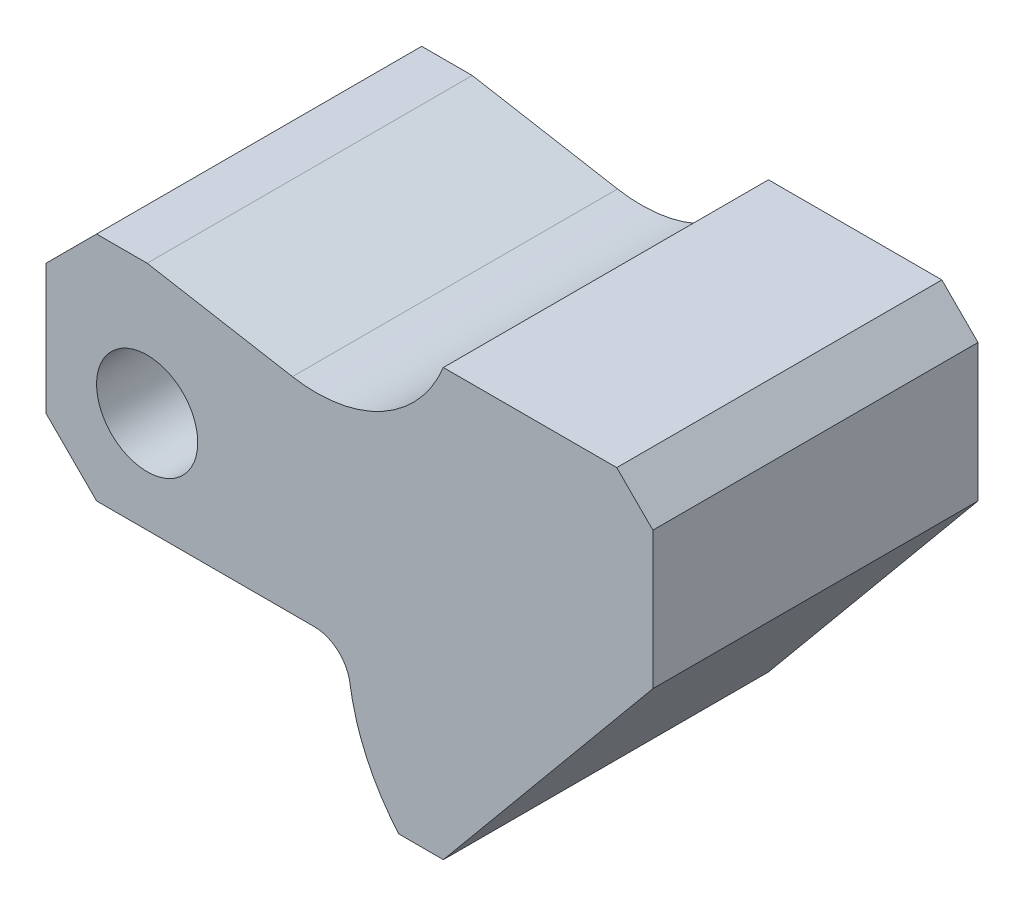
SolidWorks part; units mm, degrees
material "AISI 1020"
ref_plane "Front Plane" through (0, 0, 0) normal (0, 0, 1) x (1, 0, 0)
ref_plane "Top Plane" through (0, 0, 0) normal (0, 1, 0) x (1, 0, 0)
ref_plane "Right Plane" through (0, 0, 0) normal (1, 0, 0) x (0, 0, -1)
sketch "Sketch1" plane through (0, 0, 0) normal (0, 0, 1) x (1, 0, 0)
  line L1 (-7, -14) -> (23.1125, -14)
  line L2 (34.834, -33) -> (41, -33)
  line L3 (41, -33) -> (70, 2)
  line L4 (70, 2) -> (70, 21)
  line L5 (65, 26) -> (41, 26)
  line L6 (20.104, 14.4551) -> (0, 18)
  line L7 (0, 18) -> (-7, 18)
  line L9 (-14, 11) -> (-14, -7)
  line L10 (-7, 18) -> (-14, 11)
  line L11 (-14, -7) -> (-7, -14)
  line L12 (70, 21) -> (65, 26)
  arc A0 (23.1125, -14) -> (28.0582, -18.2647) centre (23.1125, -19) cw
  arc A1 (28.0582, -18.2647) -> (34.834, -33) centre (56.7429, -14) ccw
  circle A7 centre (0, 0) radius 7
  arc A8 (20.104, 14.4551) -> (41, 26) centre (23.4034, 33.1665) ccw
  point P1 (-14, -14)
  point P10 (70, 26)
  point P12 (0, 0)
  point P19 (-14, 18)
  dimension "D12" = 14
  dimension "D16" = 29
  dimension "D19" = 5
  dimension "D7" = 19
  dimension "D1" = 32
  dimension "D2" = 84
  dimension "D3" = 29
  dimension "D4" = 10
  dimension "D8" = 29
  dimension "D9" = 19
  dimension "D11" = 59
  dimension "D13" = 14
  dimension "D14" = 14
  dimension "D15" = 14
  dimension "D17" = 19
  dimension "D18" = 24
extrude "Boss-Extrude1" add sketch "Sketch1" along normal blind 45
equation "\"A\" = 84"
equation "\"B\" = 59"
equation "\"C\"= 45"
equation "\"D2@Sketch1\"=\"A\""
equation "\"D11@Sketch1\"=\"B\""
equation "\"D1@Boss-Extrude1\"=\"C\""
